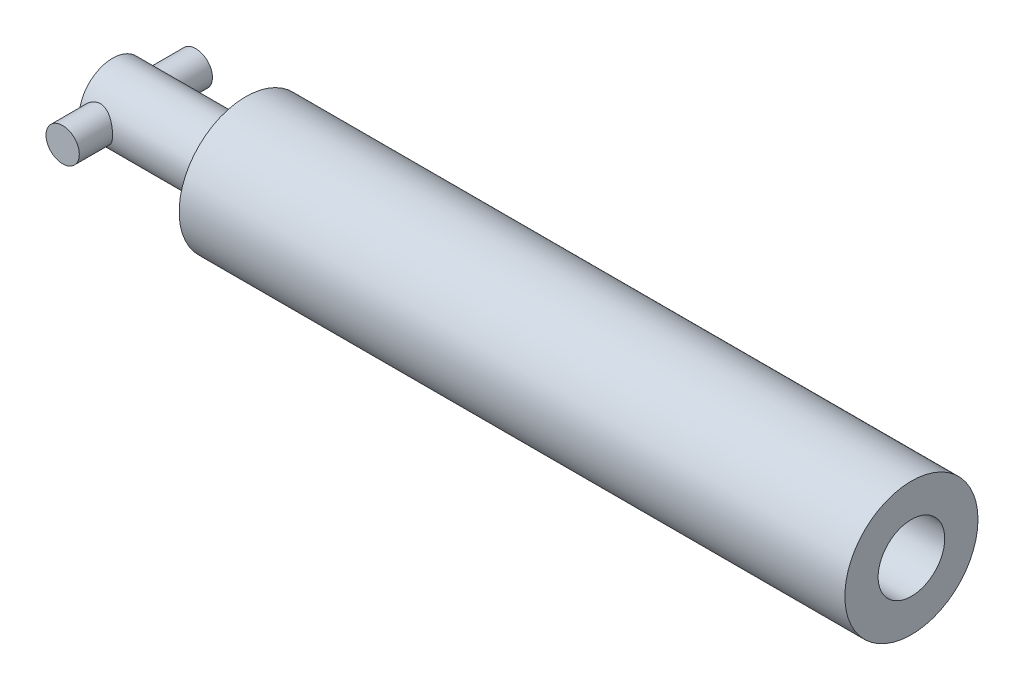
SolidWorks part; units mm, degrees
material "6061-T6 (SS)"
ref_plane "Front Plane" through (0, 0, 0) normal (0, 0, 1) x (1, 0, 0)
ref_plane "Top Plane" through (0, 0, 0) normal (0, 1, 0) x (1, 0, 0)
ref_plane "Right Plane" through (0, 0, 0) normal (1, 0, 0) x (0, 0, -1)
sketch "Sketch1" plane through (0, 0, 0) normal (1, 0, 0) x (0, 0, -1)
  circle A0 centre (0, 0) radius 25.4
  dimension "D1" = 50.8
extrude "Boss-Extrude1" add sketch "Sketch1" along normal mid plane 254
sketch "Sketch2" plane through (-127, 0, 0) normal (-1, 0, 0) x (0, 0, 1)
  circle A0 centre (0, 0) radius 12.7
  dimension "D1" = 25.4
extrude "Boss-Extrude2" add sketch "Sketch2" along normal blind 50.8
sketch "Sketch3" plane through (0, 0, 0) normal (0, 0, 1) x (1, 0, 0)
  line L0 (-177.8, 12.7) -> (-177.8, -12.7) construction
  circle A0 centre (-171.45, 0) radius 6.35
  dimension "D1" = 12.7
extrude "Boss-Extrude3" add sketch "Sketch3" along normal mid plane 50.8
sketch "Sketch4" plane through (127, 0, 0) normal (1, 0, 0) x (0, 0, -1)
  circle A0 centre (0, 0) radius 12.7
  dimension "D1" = 25.4
extrude "Cut-Extrude1" cut sketch "Sketch4" against normal blind 228.6
ref_point "Point1"
